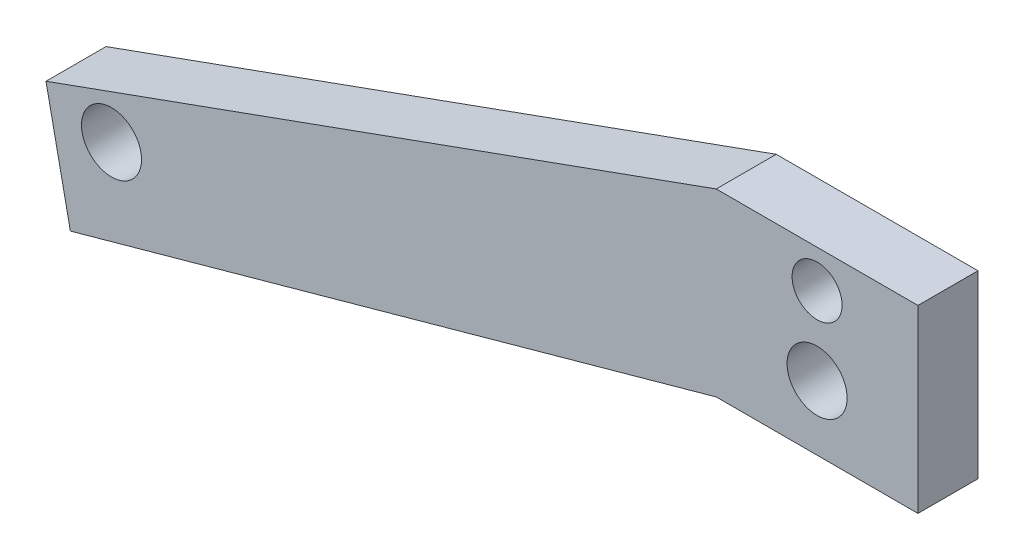
SolidWorks part; units mm, degrees
ref_plane "Front Plane" through (0, 0, 0) normal (0, 0, 1) x (1, 0, 0)
ref_plane "Top Plane" through (0, 0, 0) normal (0, 1, 0) x (1, 0, 0)
ref_plane "Right Plane" through (0, 0, 0) normal (1, 0, 0) x (0, 0, -1)
sketch "Sketch1" plane through (0, 0, 0) normal (0, 0, 1) x (1, 0, 0)
  line L0 (-16, 45) -> (-122.3101, 6.6416)
  line L2 (-276.7879, -13.7825) -> (-251.7788, -35.3347) construction
  line L3 (0, 26.6476) -> (-111.9216, 3.4517) construction
  line L4 (-16, 45) -> (-16, 15)
  line L5 (-16, 15) -> (16, 15)
  line L6 (16, 15) -> (16, 45)
  line L7 (16, 45) -> (-16, 45)
  line L8 (-16, 45) -> (-16, 16.425) construction
  line L9 (-16, 15) -> (16, 15) construction
  line L10 (16, 16.425) -> (16, 45)
  line L11 (16, 45) -> (-16, 45)
  line L12 (16, 16.425) -> (-16, 16.425)
  line L13 (-16, 16.425) -> (-118.4441, -12.012)
  line L14 (-118.4441, -12.012) -> (-122.3101, 6.6416)
  line L15 (-251.7788, -35.3347) -> (-242.2031, -37.4927) construction
  line L17 (-34.4542, 26.6396) -> (-34.1116, 26.7) construction
  line L18 (-2123.2307, -341.6) -> (-34.1116, 26.7) construction
  line L19 (-242.2031, -37.4927) -> (-208.8903, -37.4927) construction
  line L20 (-208.8903, -37.4927) -> (-16, 45) construction
  line L21 (-292.5067, -43.5335) -> (-248.9466, -55.1606) construction
  line L22 (-248.9466, -55.1606) -> (-208.8903, -56.2396) construction
  line L23 (-208.8903, -56.2396) -> (-14.9476, 16.425) construction
  line L24 (-288.0555, -26.8574) -> (0, 26.6476) construction
  circle A0 centre (0, 39) radius 3.9687 construction
  circle A1 centre (0, 39) radius 3.9688
  circle A2 centre (0, 26.6476) radius 4.7625
  circle A3 centre (-111.9216, 3.4517) radius 4.7625
  circle A4 centre (-288.0555, -26.8574) radius 17.26 construction
  dimension "D2" = 9.525
  dimension "D4" = 114.3
  dimension "D7" = 292.9825
  dimension "D3" = 9.525
  dimension "D5" = 19.05
  dimension "D6" = 28.575
  dimension "D8" = 11.709
  dimension "D9" = 160.16
  dimension "D10" = 164.486
  dimension "D1" = 0
extrude "Boss-Extrude1" add sketch "Sketch1" along normal blind 9.525
